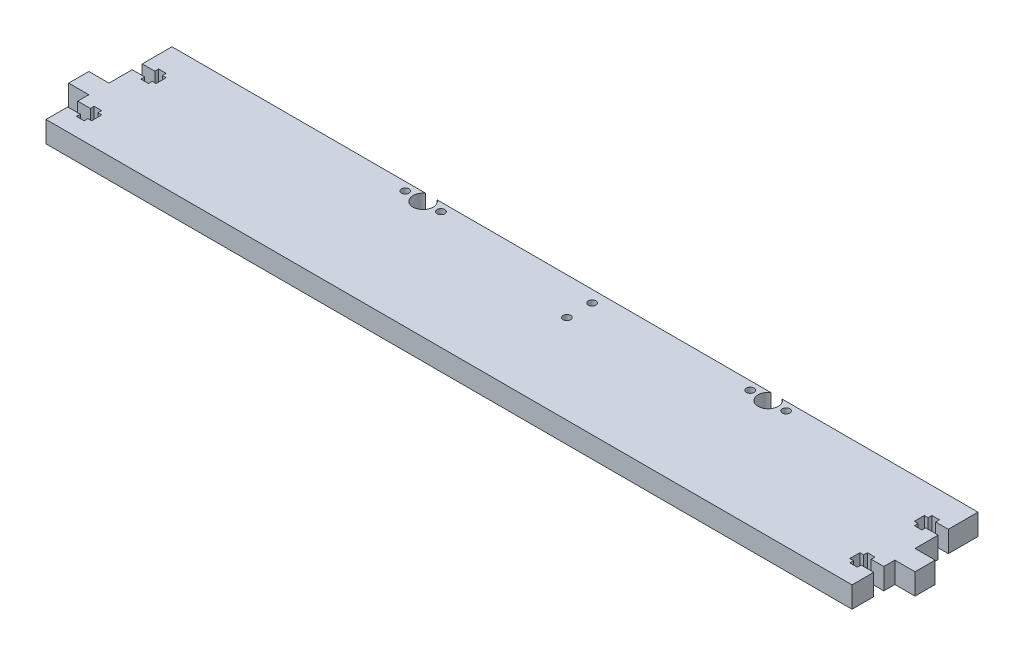
SolidWorks part; units mm, degrees
ref_plane "Front Plane" through (0, 0, 0) normal (0, 0, 1) x (1, 0, 0)
ref_plane "Top Plane" through (0, 0, 0) normal (0, 1, 0) x (1, 0, 0)
ref_plane "Right Plane" through (0, 0, 0) normal (1, 0, 0) x (0, 0, -1)
sketch "Sketch1" plane through (0, 0, 0) normal (0, 1, 0) x (1, 0, 0)
  line L0 (11.5, 25) -> (11.5, -25) construction
  line L1 (-160, 25) -> (-59.2605, 25)
  line L2 (-160, 25) -> (-160, 13.2)
  line L3 (-160, -25) -> (160, -25)
  line L4 (160, 25) -> (160, 13.2)
  line L5 (-160, 25) -> (160, -25) construction
  line L6 (-160, -25) -> (160, 25) construction
  line L7 (80, 25.7) -> (80, 17.7) construction
  line L8 (72.9, 21.7) -> (87.1, 21.7) construction
  line L9 (82.2605, 25) -> (160, 25)
  line L10 (160, 0) -> (168, 0)
  line L11 (168, 0) -> (168, -8)
  line L12 (168, -8) -> (160, -8)
  line L13 (160, -8) -> (160, -12.4)
  line L14 (160, 11.2) -> (150.5, 11.2) construction
  line L15 (160, 13.2) -> (155, 13.2)
  line L16 (155, 13.2) -> (155, 14.7)
  line L17 (155, 14.7) -> (152, 14.7)
  line L18 (152, 14.7) -> (152, 13.2)
  line L19 (152, 13.2) -> (150.5, 13.2)
  line L20 (150.5, 13.2) -> (150.5, 9.2)
  line L21 (152, 13.2) -> (155, 13.2) construction
  line L22 (152, 9.2) -> (155, 9.2) construction
  line L23 (152, 9.2) -> (150.5, 9.2)
  line L24 (152, 7.7) -> (152, 9.2)
  line L25 (155, 7.7) -> (152, 7.7)
  line L26 (155, 9.2) -> (155, 7.7)
  line L27 (160, 9.2) -> (155, 9.2)
  line L28 (160, 9.2) -> (160, 0)
  line L29 (160, -1.6) -> (150.5, -1.6) construction
  line L30 (152, -12.4) -> (155, -12.4) construction
  line L31 (152, -16.4) -> (155, -16.4) construction
  line L32 (160, -14.4) -> (150.5, -14.4) construction
  line L33 (160, -12.4) -> (155, -12.4)
  line L34 (155, -12.4) -> (155, -10.9)
  line L35 (155, -10.9) -> (152, -10.9)
  line L36 (152, -10.9) -> (152, -12.4)
  line L37 (152, -12.4) -> (150.5, -12.4)
  line L38 (150.5, -16.4) -> (150.5, -12.4)
  line L39 (152, -16.4) -> (150.5, -16.4)
  line L40 (152, -17.9) -> (152, -16.4)
  line L41 (155, -17.9) -> (152, -17.9)
  line L42 (155, -16.4) -> (155, -17.9)
  line L43 (160, -16.4) -> (155, -16.4)
  line L44 (160, -16.4) -> (160, -25)
  line L45 (-49.9, 21.7) -> (-64.1, 21.7) construction
  line L46 (-57, 25.7) -> (-57, 17.7) construction
  line L47 (0, -25) -> (0, 25) construction
  line L48 (-160, -14.4) -> (-150.5, -14.4) construction
  line L49 (-152, -16.4) -> (-155, -16.4) construction
  line L50 (-152, -12.4) -> (-155, -12.4) construction
  line L51 (-160, -1.6) -> (-150.5, -1.6) construction
  line L52 (-152, 9.2) -> (-155, 9.2) construction
  line L53 (-152, 13.2) -> (-155, 13.2) construction
  line L54 (-160, 11.2) -> (-150.5, 11.2) construction
  line L55 (-160, -16.4) -> (-160, -25)
  line L56 (-160, -16.4) -> (-155, -16.4)
  line L57 (-155, -16.4) -> (-155, -17.9)
  line L58 (-155, -17.9) -> (-152, -17.9)
  line L59 (-152, -17.9) -> (-152, -16.4)
  line L60 (-152, -16.4) -> (-150.5, -16.4)
  line L61 (-150.5, -16.4) -> (-150.5, -12.4)
  line L62 (-152, -12.4) -> (-150.5, -12.4)
  line L63 (-152, -10.9) -> (-152, -12.4)
  line L64 (-155, -10.9) -> (-152, -10.9)
  line L65 (-155, -12.4) -> (-155, -10.9)
  line L66 (-160, -12.4) -> (-155, -12.4)
  line L67 (-160, 9.2) -> (-160, 0)
  line L68 (-160, 9.2) -> (-155, 9.2)
  line L69 (-155, 9.2) -> (-155, 7.7)
  line L70 (-155, 7.7) -> (-152, 7.7)
  line L71 (-152, 7.7) -> (-152, 9.2)
  line L72 (-152, 9.2) -> (-150.5, 9.2)
  line L73 (-150.5, 13.2) -> (-150.5, 9.2)
  line L74 (-152, 13.2) -> (-150.5, 13.2)
  line L75 (-152, 14.7) -> (-152, 13.2)
  line L76 (-155, 14.7) -> (-152, 14.7)
  line L77 (-155, 13.2) -> (-155, 14.7)
  line L78 (-160, 13.2) -> (-155, 13.2)
  line L79 (-160, -8) -> (-160, -12.4)
  line L80 (-168, -8) -> (-160, -8)
  line L81 (-168, 0) -> (-168, -8)
  line L82 (-160, 0) -> (-168, 0)
  line L83 (-160, 25) -> (-160, 13.2)
  line L84 (-160, 9.2) -> (-160, 0)
  line L85 (-160, -8) -> (-160, -12.4)
  line L86 (-160, -16.4) -> (-160, -25)
  line L87 (-54.7395, 25) -> (77.7395, 25)
  line L88 (168, -4) -> (160, -4) construction
  circle A0 centre (11.5, 20.3) radius 1.5
  circle A1 centre (11.5, 10.3) radius 1.5
  arc A2 (77.7395, 25) -> (82.2605, 25) centre (80, 21.7) ccw
  circle A3 centre (87.1, 21.7) radius 1.5
  circle A4 centre (72.9, 21.7) radius 1.5
  circle A5 centre (-49.9, 21.7) radius 1.5
  circle A6 centre (-64.1, 21.7) radius 1.5
  arc A7 (-54.7395, 25) -> (-59.2605, 25) centre (-57, 21.7) cw
  point P0 (0, 0)
  dimension "D3" = 3
  dimension "D4" = 3
  dimension "D8" = 8
  dimension "D9" = 3
  dimension "D1" = 320
  dimension "D2" = 50
  dimension "D5" = 10
  dimension "D6" = 4.7
  dimension "D7" = 148.5
  dimension "D10" = 7.1
  dimension "D11" = 3.3
  dimension "D12" = 80
  dimension "D13" = 8
  dimension "D14" = 8
  dimension "D15" = 25
  dimension "D16" = 2
  dimension "D17" = 3
  dimension "D18" = 1.5
  dimension "D19" = 1.5
  dimension "D20" = 5
  dimension "D21" = 11.8
  dimension "D22" = 8.6
extrude "Boss-Extrude1" add sketch "Sketch1" along normal blind 8.4 contours L87 A7 L1 L2 L78 L77 L76 L75 L74 L73 L72 L71 L70 L69 L68 L67 L82 L81 L80 L79 L66 L65 L64 L63 L62 L61 L60 L59 L58 L57 L56 L55 L3 L44 L43 L42 L41 L40 L39 L38 L37 L36 L35 L34 L33 L13 L12 L11 L10 L28 L27
